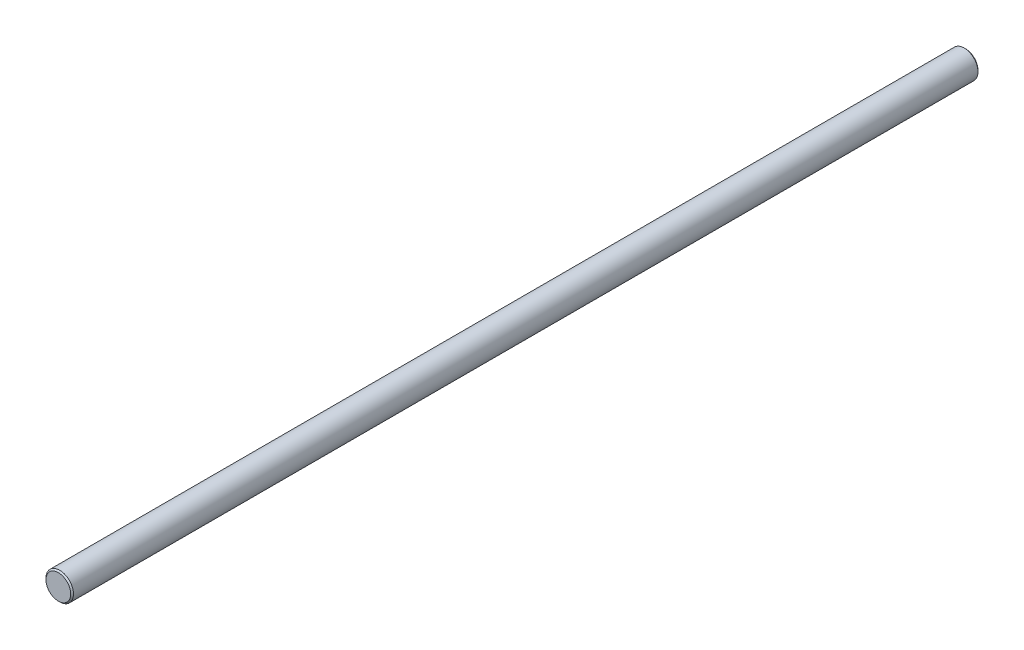
SolidWorks part; units mm, degrees
material "AISI 304"
ref_plane "Front Plane" through (0, 0, 0) normal (0, 0, 1) x (1, 0, 0)
ref_plane "Top Plane" through (0, 0, 0) normal (0, 1, 0) x (1, 0, 0)
ref_plane "Right Plane" through (0, 0, 0) normal (1, 0, 0) x (0, 0, -1)
sketch "Sketch1" plane through (0, 0, 0) normal (0, 0, 1) x (1, 0, 0)
  circle A0 centre (0, 0) radius 5
  dimension "D1" = 10
extrude "Boss-Extrude1" add sketch "Sketch1" against normal blind 330
cosmetic thread "Cosmetic Thread1" parameters "D2"=6.619
chamfer "Chamfer1" distance 0.5 angle 45 2 edges at (5, 0, -330) (5, 0, 0)
